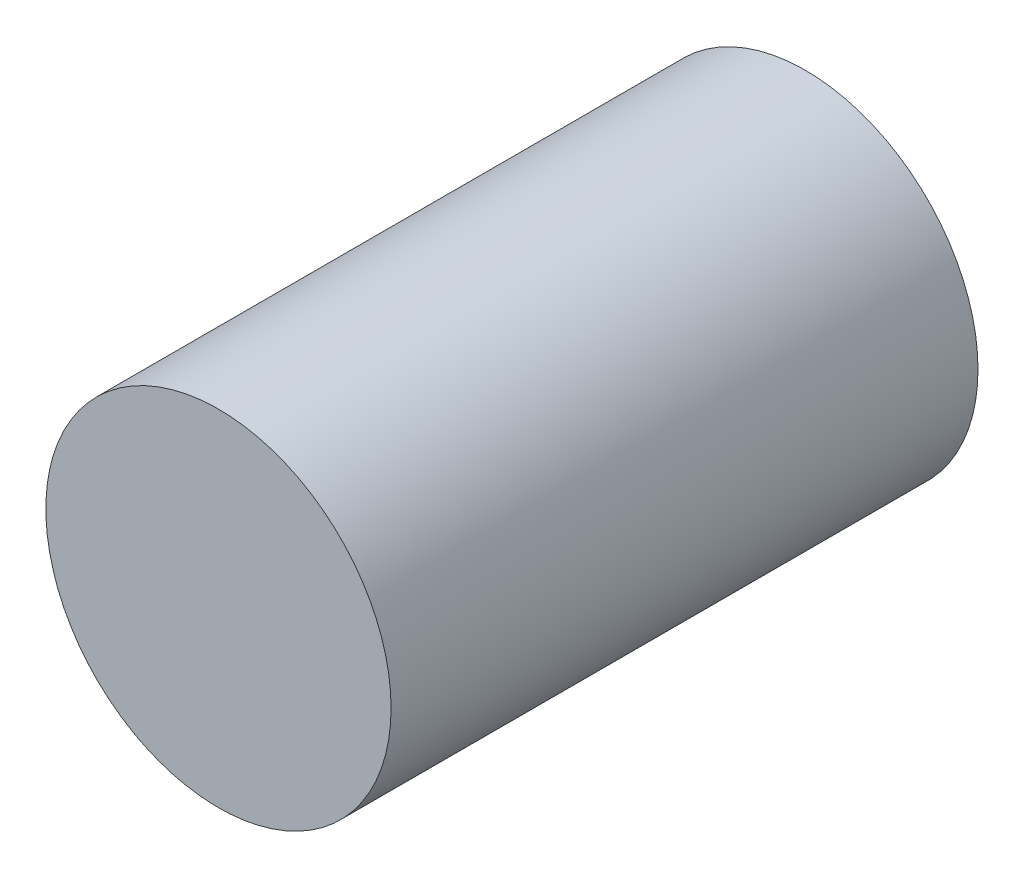
SolidWorks part; units mm, degrees
ref_plane "Plan de face" through (0, 0, 0) normal (0, 0, 1) x (1, 0, 0)
ref_plane "Plan de dessus" through (0, 0, 0) normal (0, 1, 0) x (1, 0, 0)
ref_plane "Plan de droite" through (0, 0, 0) normal (1, 0, 0) x (0, 0, -1)
sketch "Esquisse1" plane through (0, 0, 0) normal (0, 0, 1) x (1, 0, 0)
  circle A0 centre (0, 0) radius 25
  dimension "D1" = 50
extrude "Boss.-Extru.1" add sketch "Esquisse1" along normal blind 85
ref_plane "Plan1" through (0, 0, 5) normal (0, 0, -1) x (-1, 0, 0)
sketch "Esquisse2" plane through (0, 0, 5) normal (0, 0, -1) x (-1, 0, 0)
  circle A0 centre (0, 0) radius 5
  dimension "D1" = 10
curve "Hélice/Spirale1"
ref_plane "Plan2" through (0, 0, 80) normal (0, 0, 1) x (1, 0, 0)
sketch "Esquisse4" plane through (0, 0, 80) normal (0, 0, 1) x (1, 0, 0)
  circle A0 centre (0, 0) radius 20
  dimension "D1" = 40
curve "Hélice/Spirale2" parameters "D10001"=75, "D30001"=40, "D40001"=20, "D50000"=30
sketch3d "Esquisse3D5"
  spline S0 degree 3 poles (-1739.0962, 986.9703, 5) (-2.2011, -154.6453, 5) (22.054, 5.7386, 5) (-3.1098, 5.4768, 5) (-4.004, 5.2767, 5) (-5.7187, 4.446, 5) (-6.5377, 3.8149, 5) (-7.8979, 2.1645, 5) (-8.4375, 1.1454, 5) (-9.0625, -1.1454, 5) (-9.1466, -2.4161, 5) (-8.7535, -4.9984, 5) (-8.2755, -6.3086, 5) (-6.7505, -8.7174, 5) (-5.7035, -9.8144, 5) (-3.146, -11.5503, 5) (-1.6362, -12.1875, 5) (1.6362, -12.8125, 5) (3.3976, -12.799, 5) (6.0146, -12.2224, 5) (6.8823, -11.9384, 5) (8.5695, -11.1869, 5) (9.3889, -10.7194, 5) (10.9404, -9.6099, 5) (11.6725, -8.9677, 5) (13.0118, -7.5258, 5) (13.619, -6.726, 5) (14.6748, -4.9937, 5) (15.1233, -4.0613, 5) (15.8328, -2.0962, 5) (16.0937, -1.0636, 5) (16.4063, 1.0636, 5) (16.4577, 2.158, 5) (16.3373, 4.3654, 5) (16.1653, 5.4783, 5) (15.593, 7.6765, 5) (15.1927, 8.7616, 5) (14.1685, 10.8569, 5) (13.5447, 11.867, 5) (12.088, 13.7656, 5) (11.2552, 14.6541, 5) (9.4051, 16.2662, 5) (8.3878, 16.9896, 5) (6.202, 18.2333, 5) (5.0336, 18.7533, 5) (-47.9512, 36.1931, 5) (-197.8612, -157.1195, 5) (1365.4811, -1425.9762, 5) knots -1.752573 -1.752573 -1.752573 -1.752573 0.0625 0.0625 0.125 0.125 0.1875 0.1875 0.25 0.25 0.3125 0.3125 0.375 0.375 0.4375 0.4375 0.5 0.5 0.5625 0.5625 0.59375 0.59375 0.625 0.625 0.65625 0.65625 0.6875 0.6875 0.71875 0.71875 0.75 0.75 0.78125 0.78125 0.8125 0.8125 0.84375 0.84375 0.875 0.875 0.90625 0.90625 0.9375 0.9375 0.96875 0.96875 2.291063 2.291063 2.291063 2.291063 only from (0, 5, 5) to (0, 20, 5) construction
  spline S1 degree 3 poles (0, 5, 5) (-0.6545, 5.3125, 5) (-1.4345, 5.4943, 5) (-3.1098, 5.4768, 5) (-4.004, 5.2767, 5) (-5.7187, 4.446, 5) (-6.5377, 3.8149, 5) (-7.8979, 2.1645, 5) (-8.4375, 1.1454, 5) (-9.0625, -1.1454, 5) (-9.1466, -2.4161, 5) (-8.7535, -4.9984, 5) (-8.2755, -6.3086, 5) (-6.7505, -8.7174, 5) (-5.7035, -9.8144, 5) (-3.146, -11.5503, 5) (-1.6362, -12.1875, 5) (1.6362, -12.8125, 5) (3.3976, -12.799, 5) (6.0146, -12.2224, 5) (6.8823, -11.9384, 5) (8.5695, -11.1869, 5) (9.3889, -10.7194, 5) (10.9404, -9.6099, 5) (11.6725, -8.9677, 5) (13.0118, -7.5258, 5) (13.619, -6.726, 5) (14.6748, -4.9937, 5) (15.1233, -4.0613, 5) (15.8328, -2.0962, 5) (16.0937, -1.0636, 5) (16.4063, 1.0636, 5) (16.4577, 2.158, 5) (16.3373, 4.3654, 5) (16.1653, 5.4783, 5) (15.593, 7.6765, 5) (15.1927, 8.7616, 5) (14.1685, 10.8569, 5) (13.5447, 11.867, 5) (12.088, 13.7656, 5) (11.2552, 14.6541, 5) (9.4051, 16.2662, 5) (8.3878, 16.9896, 5) (6.202, 18.2333, 5) (5.0336, 18.7533, 5) (2.5871, 19.5586, 5) (1.309, 19.8437, 5) (0, 20, 5) knots 0 0 0 0 0.0625 0.0625 0.125 0.125 0.1875 0.1875 0.25 0.25 0.3125 0.3125 0.375 0.375 0.4375 0.4375 0.5 0.5 0.5625 0.5625 0.59375 0.59375 0.625 0.625 0.65625 0.65625 0.6875 0.6875 0.71875 0.71875 0.75 0.75 0.78125 0.78125 0.8125 0.8125 0.84375 0.84375 0.875 0.875 0.90625 0.90625 0.9375 0.9375 0.96875 0.96875 1 1 1 1
  spline S2 degree 3 poles (1684.6478, -1037.214, 122.3717) (-213.468, -162.393, 105.4236) (-42.3244, 45.4438, 91.5694) (12.3739, 16.0557, 76.875) (14.8987, 13.7522, 76.0938) (18.5516, 8.1813, 74.5312) (19.6749, 4.9189, 73.75) (20.202, -1.7828, 72.1875) (19.6038, -5.2151, 71.4062) (16.7876, -11.3879, 69.8438) (14.5714, -14.121, 69.0625) (9.0433, -18.1644, 67.5) (5.7369, -19.469, 66.7188) (-1.1321, -20.2651, 65.1562) (-4.6869, -19.7541, 64.375) (-11.1029, -16.9975, 62.8125) (-13.9556, -14.7539, 62.0313) (-18.1601, -9.091, 60.4687) (-19.5052, -5.678, 59.6875) (-20.2661, 1.4066, 58.125) (-19.6791, 5.0689, 57.3437) (-16.6765, 11.6126, 55.7813) (-14.2633, 14.4843, 55) (-8.2486, 18.5795, 53.4375) (-4.6544, 19.7956, 52.6562) (2.6927, 20.1563, 51.0938) (6.4347, 19.2983, 50.3125) (12.9417, 15.6953, 48.75) (15.6954, 12.9539, 47.9687) (19.329, 6.3669, 46.4063) (20.2009, 2.5309, 45.625) (19.7188, -5.0644, 44.0625) (18.3631, -8.8105, 43.2813) (13.7789, -14.999, 41.7187) (10.5564, -17.4286, 40.9375) (3.2389, -20.1172, 39.375) (-0.8432, -20.3683, 38.5937) (-8.5176, -18.521, 37.0313) (-12.0938, -16.4231, 36.25) (-17.4777, -10.5124, 34.6875) (-19.2715, -6.7094, 33.9063) (-20.3634, 1.3174, 32.3437) (-19.6555, 5.5242, 31.5625) (-15.8899, 12.8205, 30) (-12.8373, 15.8912, 29.2188) (-5.431, 19.6934, 27.6562) (-1.0934, 20.4116, 26.875) (7.2506, 19.1117, 25.3125) (11.2347, 17.0921, 24.5313) (17.2508, 10.9895, 22.9687) (19.2625, 6.9193, 22.1875) (20.1129, 0.4501, 21.0156) (20.0425, -1.7612, 20.625) (19.1853, -6.0603, 19.8438) (18.3985, -8.1471, 19.4531) (16.1769, -11.9661, 18.6719) (14.7424, -13.6975, 18.2813) (11.3685, -16.6047, 17.5) (9.4298, -17.7797, 17.1094) (5.2534, -19.4279, 16.3281) (3.0165, -19.9003, 15.9375) (-1.5072, -20.0712, 15.1563) (-3.7931, -19.7692, 14.7656) (-8.1499, -18.4062, 13.9844) (-10.2198, -17.3452, 13.5938) (-13.8932, -14.5697, 12.8125) (-15.4959, -12.8557, 12.4219) (-18.0292, -8.9633, 11.6406) (-18.959, -6.7857, 11.25) (-20.0139, -2.2207, 10.4688) (-20.1385, 0.1656, 10.0781) (-19.5451, 4.8557, 9.2969) (-18.8268, 7.1583, 8.9063) (-16.615, 11.3856, 8.125) (-15.1217, 13.309, 7.7344) (-11.5309, 16.5177, 6.9531) (-9.4341, 17.8019, 6.5625) (46.2581, 39.1709, -3.0235) (194.3552, -169.8516, -12.1654) (-1599.6984, -1161.4173, -25.0343) knots -0.525277 -0.525277 -0.525277 -0.525277 0.03125 0.03125 0.0625 0.0625 0.09375 0.09375 0.125 0.125 0.15625 0.15625 0.1875 0.1875 0.21875 0.21875 0.25 0.25 0.28125 0.28125 0.3125 0.3125 0.34375 0.34375 0.375 0.375 0.40625 0.40625 0.4375 0.4375 0.46875 0.46875 0.5 0.5 0.53125 0.53125 0.5625 0.5625 0.59375 0.59375 0.625 0.625 0.65625 0.65625 0.6875 0.6875 0.71875 0.71875 0.75 0.75 0.78125 0.78125 0.796875 0.796875 0.8125 0.8125 0.828125 0.828125 0.84375 0.84375 0.859375 0.859375 0.875 0.875 0.890625 0.890625 0.90625 0.90625 0.921875 0.921875 0.9375 0.9375 0.953125 0.953125 0.96875 0.96875 0.984375 0.984375 1.352191 1.352191 1.352191 1.352191 only from (0, 20, 80) to (0, 20, 5) construction
  spline S3 degree 3 poles (0, 20, 80) (3.2733, 20, 79.2186) (6.5577, 19.1806, 78.4375) (12.3739, 16.0557, 76.875) (14.8987, 13.7522, 76.0938) (18.5516, 8.1813, 74.5312) (19.6749, 4.9189, 73.75) (20.202, -1.7828, 72.1875) (19.6038, -5.2151, 71.4062) (16.7876, -11.3879, 69.8438) (14.5714, -14.121, 69.0625) (9.0433, -18.1644, 67.5) (5.7369, -19.469, 66.7188) (-1.1321, -20.2651, 65.1562) (-4.6869, -19.7541, 64.375) (-11.1029, -16.9975, 62.8125) (-13.9556, -14.7539, 62.0313) (-18.1601, -9.091, 60.4687) (-19.5052, -5.678, 59.6875) (-20.2661, 1.4066, 58.125) (-19.6791, 5.0689, 57.3437) (-16.6765, 11.6126, 55.7813) (-14.2633, 14.4843, 55) (-8.2486, 18.5795, 53.4375) (-4.6544, 19.7956, 52.6562) (2.6927, 20.1563, 51.0938) (6.4347, 19.2983, 50.3125) (12.9417, 15.6953, 48.75) (15.6954, 12.9539, 47.9687) (19.329, 6.3669, 46.4063) (20.2009, 2.5309, 45.625) (19.7188, -5.0644, 44.0625) (18.3631, -8.8105, 43.2813) (13.7789, -14.999, 41.7187) (10.5564, -17.4286, 40.9375) (3.2389, -20.1172, 39.375) (-0.8432, -20.3683, 38.5937) (-8.5176, -18.521, 37.0313) (-12.0938, -16.4231, 36.25) (-17.4777, -10.5124, 34.6875) (-19.2715, -6.7094, 33.9063) (-20.3634, 1.3174, 32.3437) (-19.6555, 5.5242, 31.5625) (-15.8899, 12.8205, 30) (-12.8373, 15.8912, 29.2188) (-5.431, 19.6934, 27.6562) (-1.0934, 20.4116, 26.875) (7.2506, 19.1117, 25.3125) (11.2347, 17.0921, 24.5313) (17.2508, 10.9895, 22.9687) (19.2625, 6.9193, 22.1875) (20.1129, 0.4501, 21.0156) (20.0425, -1.7612, 20.625) (19.1853, -6.0603, 19.8438) (18.3985, -8.1471, 19.4531) (16.1769, -11.9661, 18.6719) (14.7424, -13.6975, 18.2813) (11.3685, -16.6047, 17.5) (9.4298, -17.7797, 17.1094) (5.2534, -19.4279, 16.3281) (3.0165, -19.9003, 15.9375) (-1.5072, -20.0712, 15.1563) (-3.7931, -19.7692, 14.7656) (-8.1499, -18.4062, 13.9844) (-10.2198, -17.3452, 13.5938) (-13.8932, -14.5697, 12.8125) (-15.4959, -12.8557, 12.4219) (-18.0292, -8.9633, 11.6406) (-18.959, -6.7857, 11.25) (-20.0139, -2.2207, 10.4688) (-20.1385, 0.1656, 10.0781) (-19.5451, 4.8557, 9.2969) (-18.8268, 7.1583, 8.9063) (-16.615, 11.3856, 8.125) (-15.1217, 13.309, 7.7344) (-11.5309, 16.5177, 6.9531) (-9.4341, 17.8019, 6.5625) (-4.8952, 19.5434, 5.7812) (-2.455, 20, 5.3907) (0, 20, 5) knots 0 0 0 0 0.03125 0.03125 0.0625 0.0625 0.09375 0.09375 0.125 0.125 0.15625 0.15625 0.1875 0.1875 0.21875 0.21875 0.25 0.25 0.28125 0.28125 0.3125 0.3125 0.34375 0.34375 0.375 0.375 0.40625 0.40625 0.4375 0.4375 0.46875 0.46875 0.5 0.5 0.53125 0.53125 0.5625 0.5625 0.59375 0.59375 0.625 0.625 0.65625 0.65625 0.6875 0.6875 0.71875 0.71875 0.75 0.75 0.78125 0.78125 0.796875 0.796875 0.8125 0.8125 0.828125 0.828125 0.84375 0.84375 0.859375 0.859375 0.875 0.875 0.890625 0.890625 0.90625 0.90625 0.921875 0.921875 0.9375 0.9375 0.953125 0.953125 0.96875 0.96875 0.984375 0.984375 1 1 1 1
  point P1 (0.6022, 19.9187, 5)
  point P7 (0, 0, 0)
